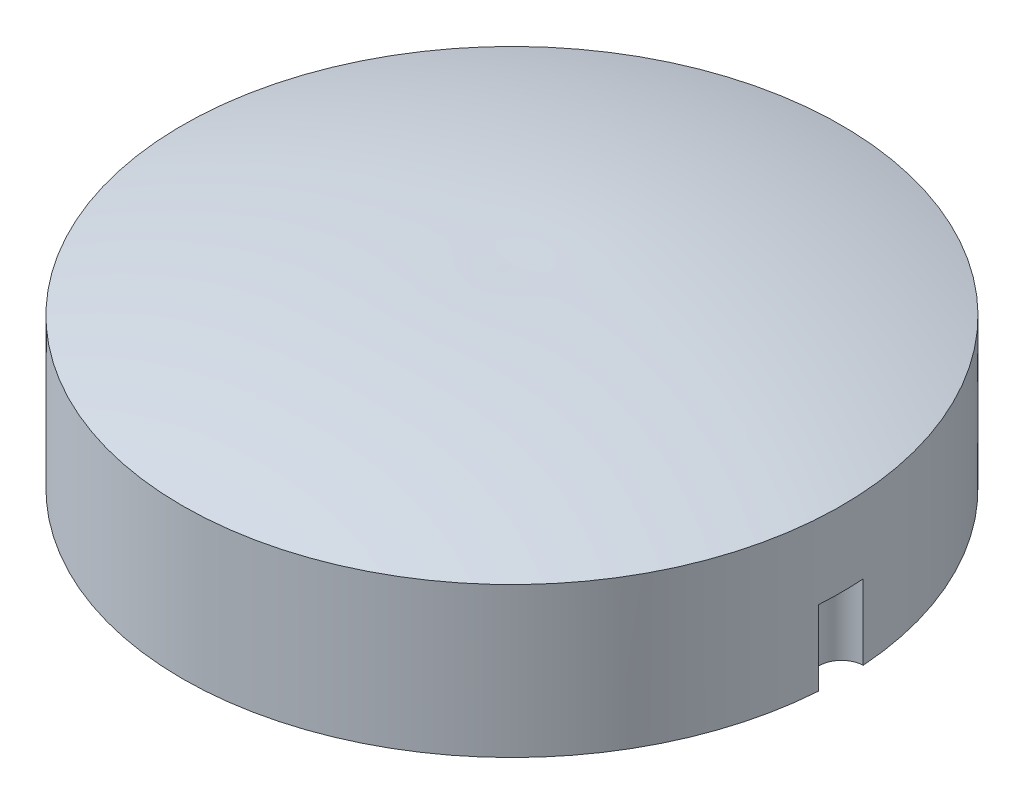
SolidWorks part; units mm, degrees
ref_plane "Front Plane" through (0, 0, 0) normal (0, 0, 1) x (1, 0, 0)
ref_plane "Top Plane" through (0, 0, 0) normal (0, 1, 0) x (1, 0, 0)
ref_plane "Right Plane" through (0, 0, 0) normal (1, 0, 0) x (0, 0, -1)
sketch "Sketch1" plane through (0, 0, 0) normal (0, 0, 1) x (1, 0, 0)
  line L0 (0, 28.305) -> (0, -23.3262) construction
  line L2 (0, 0) -> (22, 0)
  line L3 (0, 0) -> (0, 13)
  line L5 (22, 0) -> (22, 10)
  arc A0 (0, 13) -> (22, 10) centre (2.4263, -51.3737) cw
  dimension "D1" = 13
  dimension "D2" = 3
  dimension "D3" = 44
revolve "Revolve2" add sketch "Sketch1" angle 360 about L0
sketch "Sketch3" plane through (0, 0, 0) normal (0, -1, 0) x (1, 0, 0)
  circle A0 centre (22, 0) radius 1.5
  dimension "D1" = 22
  dimension "D2" = 3
extrude "Cut-Extrude1" cut sketch "Sketch3" against normal blind 5
